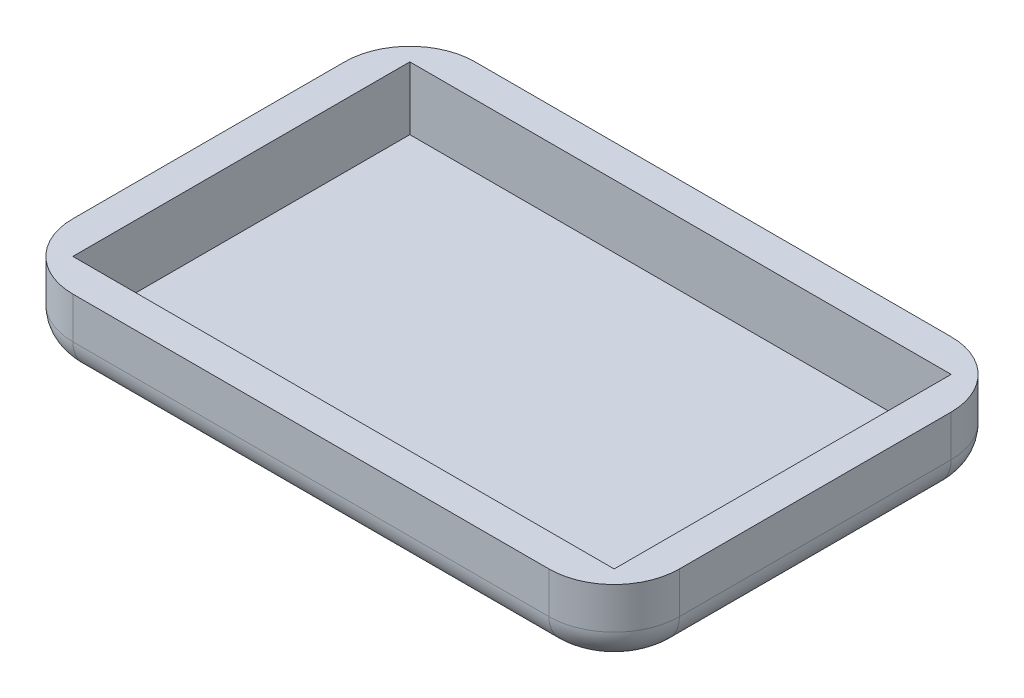
SolidWorks part; units mm, degrees
ref_plane "Front Plane" through (0, 0, 0) normal (0, 0, 1) x (1, 0, 0)
ref_plane "Top Plane" through (0, 0, 0) normal (0, 1, 0) x (1, 0, 0)
ref_plane "Right Plane" through (0, 0, 0) normal (1, 0, 0) x (0, 0, -1)
sketch "Sketch1" plane through (0, 0, 0) normal (0, 1, 0) x (1, 0, 0)
  line L1 (0, 0) -> (70.866, 0)
  line L2 (0, 0) -> (0, 46.99)
  line L3 (0, 46.99) -> (70.866, 46.99)
  line L4 (70.866, 0) -> (70.866, 46.99)
  dimension "D1" = 46.99
  dimension "D2" = 70.866
extrude "Boss-Extrude1" add sketch "Sketch1" along normal blind 8.636
sketch "Sketch2" plane through (0, 8.636, 0) normal (0, 1, 0) x (1, 0, 0)
  line L0 (0, 23.495) -> (70.866, 23.495) construction
  line L1 (0, 46.99) -> (0, 0) construction
  line L2 (70.866, 0) -> (70.866, 46.99) construction
  line L4 (3.81, 3.81) -> (67.056, 3.81)
  line L5 (3.81, 3.81) -> (3.81, 43.18)
  line L6 (3.81, 43.18) -> (67.056, 43.18)
  line L7 (67.056, 3.81) -> (67.056, 43.18)
  line L8 (3.81, 3.81) -> (67.056, 43.18) construction
  line L9 (3.81, 43.18) -> (67.056, 3.81) construction
  point P6 (35.433, 23.495)
  dimension "D1" = 39.37
  dimension "D2" = 63.246
extrude "Cut-Extrude1" cut sketch "Sketch2" against normal blind 7.366
fillet "Fillet2" radius 7.62 4 edges at (70.866, 4.318, -46.99) (70.866, 4.318, 0) (0, 4.318, 0) (0, 4.318, -46.99)
fillet "Fillet3" radius 3.81 8 edges at (68.6342, 0, -44.7582) (70.866, 0, -23.495) (68.6342, 0, -2.2318) (35.433, 0, 0) (2.2318, 0, -2.2318) (0, 0, -23.495) (2.2318, 0, -44.7582) (35.433, 0, -46.99)
